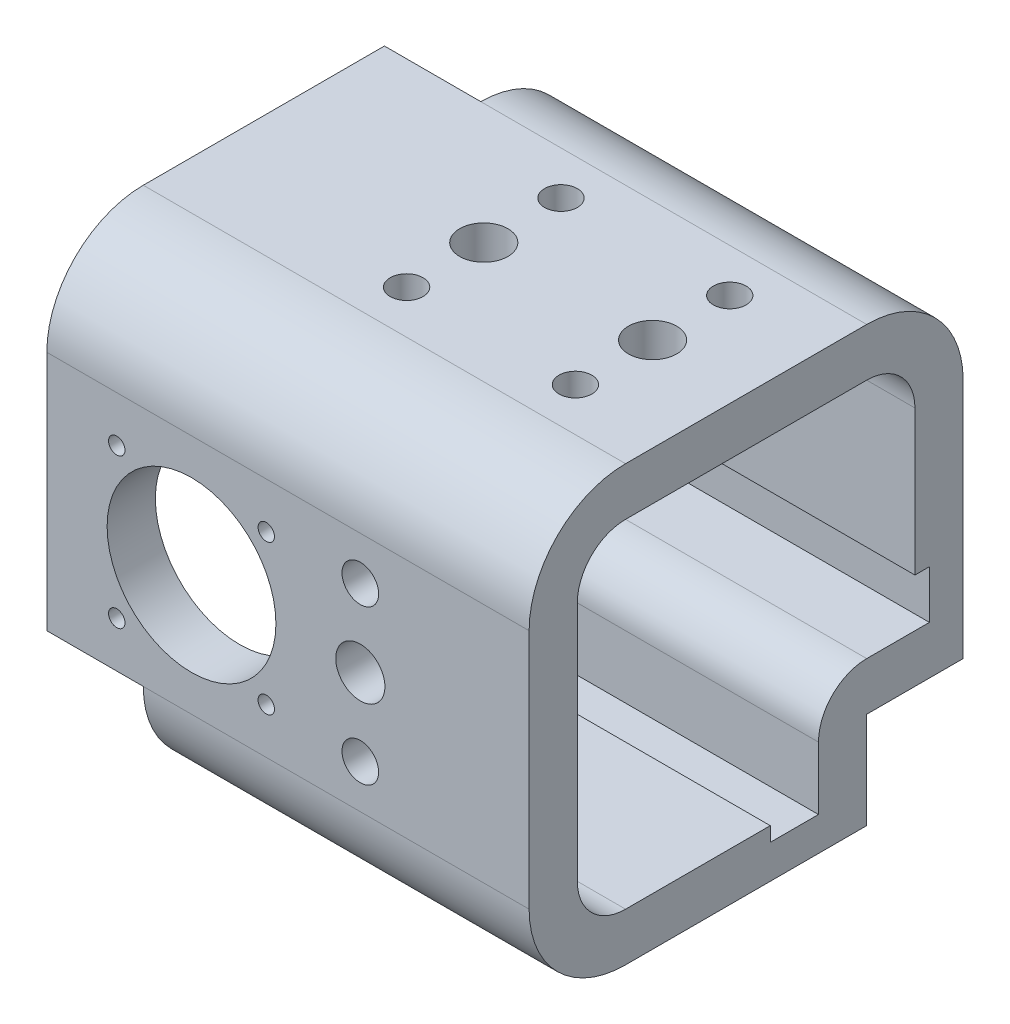
SolidWorks part; units mm, degrees
material "ABS"
ref_plane "Front Plane" through (0, 0, 0) normal (0, 0, 1) x (1, 0, 0)
ref_plane "Top Plane" through (0, 0, 0) normal (0, 1, 0) x (1, 0, 0)
ref_plane "Right Plane" through (0, 0, 0) normal (1, 0, 0) x (0, 0, -1)
sketch "Sketch2" plane through (0, 0, 0) normal (1, 0, 0) x (0, 0, -1)
  line L0 (3374.6539, 80.8979) -> (3374.6539, 76.9979) construction
  line L1 (3434.6539, 129.4479) -> (3384.6539, 129.4479)
  line L2 (3444.6539, 119.4479) -> (3444.6539, 69.4479)
  line L3 (3434.6539, 59.4479) -> (3384.6539, 59.4479)
  line L4 (3374.6539, 119.4479) -> (3374.6539, 69.4479)
  line L5 (-50.8, 109.4479) -> (3374.6539, 109.4479) construction
  line L10 (3367.4039, 109.4479) -> (3356.4039, 109.4479) construction
  line L11 (-50.8, 79.4479) -> (3374.6539, 79.4479) construction
  line L12 (3356.4039, 79.4479) -> (3367.4039, 79.4479) construction
  line L13 (3434.6539, 139.4479) -> (3384.6539, 139.4479)
  line L14 (3364.6539, 119.4479) -> (3364.6539, 69.4479)
  line L15 (3434.6539, 49.4479) -> (3384.6539, 49.4479)
  line L16 (3454.6539, 119.4479) -> (3454.6539, 69.4479)
  line L19 (3375.4039, 73.2979) -> (3386.4039, 73.2979) construction
  arc A0 (3384.6539, 129.4479) -> (3374.6539, 119.4479) centre (3384.6539, 119.4479) ccw
  arc A1 (3384.6539, 59.4479) -> (3374.6539, 69.4479) centre (3384.6539, 69.4479) cw
  arc A2 (3434.6539, 59.4479) -> (3444.6539, 69.4479) centre (3434.6539, 69.4479) ccw
  arc A3 (3434.6539, 129.4479) -> (3444.6539, 119.4479) centre (3434.6539, 119.4479) cw
  arc A4 (3384.6539, 139.4479) -> (3364.6539, 119.4479) centre (3384.6539, 119.4479) ccw
  arc A5 (3384.6539, 49.4479) -> (3364.6539, 69.4479) centre (3384.6539, 69.4479) cw
  arc A6 (3434.6539, 49.4479) -> (3454.6539, 69.4479) centre (3434.6539, 69.4479) ccw
  arc A7 (3434.6539, 139.4479) -> (3454.6539, 119.4479) centre (3434.6539, 119.4479) cw
  arc A8 (3434.6539, 129.4479) -> (3444.6539, 119.4479) centre (3434.6539, 119.4479) cw construction
  dimension "D1" = 10
  dimension "D2" = 10
  dimension "D3" = 3.85
  dimension "D4" = 70
extrude "Boss-Extrude1" add sketch "Sketch2" along normal blind 70 and the other way blind 30
sketch "Sketch3" plane through (0, 0, -3364.6539) normal (0, 0, 1) x (1, 0, 0)
  arc A0 (-14.0466, 99.7104) -> (-13.6647, 100.6346) centre (0, 94.4479) ccw construction
  arc A1 (-14.0466, 99.7104) -> (-13.6647, 100.6346) centre (0, 94.4479) ccw construction
  circle A2 centre (15.5, 78.9479) radius 1.7 construction
  circle A3 centre (15.5, 109.9479) radius 1.7 construction
  circle A4 centre (-15.5, 109.9479) radius 1.7 construction
  circle A5 centre (-15.5, 78.9479) radius 1.7 construction
  circle A6 centre (15.5, 78.9479) radius 1.7
  circle A7 centre (15.5, 109.9479) radius 1.7
  circle A8 centre (-15.5, 109.9479) radius 1.7
  circle A9 centre (-15.5, 78.9479) radius 1.7
  circle A10 centre (0, 94.4479) radius 17.5
  arc A11 (-16.3877, 100.5874) -> (-15.9422, 101.6657) centre (0, 94.4479) ccw construction
  circle A12 centre (35, 94.4479) radius 5.1 construction
  circle A13 centre (35, 94.4479) radius 5.1
  circle A14 centre (35, 78.4479) radius 3.8 construction
  circle A15 centre (35, 110.4479) radius 3.8 construction
  circle A16 centre (35, 78.4479) radius 3.8
  circle A17 centre (35, 110.4479) radius 3.8
  dimension "D1" = 2.5
extrude "Cut-Extrude1" cut sketch "Sketch3" against normal up to next
sketch "Sketch4" plane through (0, 139.4479, 0) normal (0, 1, 0) x (1, 0, 0)
  line L0 (50.6, 3409.6539) -> (15.6, 3409.6539) construction
  line L1 (-30, 3434.6539) -> (70, 3434.6539) construction
  line L2 (-30, 3384.6539) -> (70, 3384.6539) construction
  line L3 (28.05, 3396.5539) -> (38.15, 3396.5539) construction
  line L4 (28.05, 3396.5539) -> (38.15, 3396.5539) construction
  line L5 (33.1, 3396.5539) -> (33.1, 3409.6539) construction
  circle A0 centre (15.6, 3409.6539) radius 5
  circle A1 centre (50.6, 3409.6539) radius 5
  circle A2 centre (50.6, 3425.6539) radius 3.4 construction
  circle A3 centre (50.6, 3393.6539) radius 3.4 construction
  circle A4 centre (15.6, 3425.6539) radius 3.4 construction
  circle A5 centre (15.6, 3393.6539) radius 3.4 construction
  circle A6 centre (50.6, 3425.6539) radius 3.4
  circle A7 centre (50.6, 3393.6539) radius 3.4
  circle A8 centre (15.6, 3425.6539) radius 3.4
  circle A9 centre (15.6, 3393.6539) radius 3.4
  point P12 (33.1, 3409.6539)
  dimension "D1" = 10
  dimension "D2" = 35
extrude "Cut-Extrude2" cut sketch "Sketch4" against normal up to next
sketch "Sketch5" plane through (0, 0, -3364.6539) normal (0, 0, 1) x (1, 0, 0)
  line L0 (-30, 69.4479) -> (70, 69.4479) construction
  line L1 (-10, 69.4479) -> (-30, 69.4479)
  line L2 (-10, 69.4479) -> (-10, 49.4479)
  line L3 (-10, 49.4479) -> (-30, 49.4479)
  line L4 (-30, 69.4479) -> (-30, 49.4479)
  line L5 (-30, 119.4479) -> (-30, 69.4479) construction
  line L6 (-30, 49.4479) -> (70, 49.4479) construction
  dimension "D1" = 20
extrude "Cut-Extrude3" cut sketch "Sketch5" against normal through all both and the other way through all
sketch "Sketch6" plane through (0, 139.4479, 0) normal (0, 1, 0) x (1, 0, 0)
  line L0 (-30, 3434.6539) -> (-30, 3384.6539) construction
  line L1 (-30, 3454.6539) -> (-10, 3454.6539)
  line L2 (-30, 3454.6539) -> (-30, 3434.6539)
  line L3 (-30, 3434.6539) -> (-10, 3434.6539)
  line L4 (-10, 3454.6539) -> (-10, 3434.6539)
  line L5 (-30, 3434.6539) -> (70, 3434.6539) construction
  line L6 (-30, 3454.6539) -> (70, 3454.6539) construction
  dimension "D1" = 20
extrude "Cut-Extrude4" cut sketch "Sketch6" against normal through all
sketch "Sketch7" plane through (-10, 0, 0) normal (-1, 0, 0) x (0, 0, 1)
  line L10 (-3434.6539, 49.4479) -> (-3384.6539, 49.4479) construction
  line L11 (-3454.6539, 69.4479) -> (-3434.6539, 69.4479)
  line L12 (-3454.6539, 69.4479) -> (-3454.6539, 49.4479)
  line L13 (-3454.6539, 49.4479) -> (-3434.6539, 49.4479)
  line L14 (-3434.6539, 69.4479) -> (-3434.6539, 49.4479)
  line L15 (-3454.6539, 69.4479) -> (-3454.6539, 119.4479) construction
  line L16 (-3444.6539, 119.4479) -> (-3444.6539, 69.4479) construction
  line L17 (-3444.6539, 89.4479) -> (-3447.6539, 89.4479)
  line L18 (-3444.6539, 89.4479) -> (-3444.6539, 69.4479)
  line L19 (-3444.6539, 69.4479) -> (-3447.6539, 69.4479)
  line L20 (-3447.6539, 89.4479) -> (-3447.6539, 69.4479)
  line L21 (-3434.6539, 59.4479) -> (-3384.6539, 59.4479) construction
  line L22 (-3434.6539, 56.4479) -> (-3414.6539, 56.4479)
  line L23 (-3434.6539, 56.4479) -> (-3434.6539, 59.4479)
  line L24 (-3434.6539, 59.4479) -> (-3414.6539, 59.4479)
  line L25 (-3414.6539, 56.4479) -> (-3414.6539, 59.4479)
  dimension "D1" = 20
  dimension "D2" = 20
  dimension "D3" = 3
extrude "Cut-Extrude5" cut sketch "Sketch7" against normal through all
sketch "Sketch8" plane through (-10, 0, 0) normal (-1, 0, 0) x (0, 0, 1)
  line L0 (-3454.6539, 79.4479) -> (-3434.6539, 79.4479)
  line L1 (-3454.6539, 69.4479) -> (-3454.6539, 119.4479) construction
  line L2 (-3424.6539, 69.4479) -> (-3424.6539, 49.4479)
  line L3 (-3434.6539, 49.4479) -> (-3384.6539, 49.4479) construction
  line L4 (-3454.6539, 69.4479) -> (-3434.6539, 69.4479)
  line L5 (-3434.6539, 69.4479) -> (-3434.6539, 49.4479)
  line L8 (-3454.6539, 79.4479) -> (-3454.6539, 69.4479)
  line L9 (-3434.6539, 49.4479) -> (-3424.6539, 49.4479)
  line L10 (-3424.6539, 79.4479) -> (-3424.6539, 49.4479) construction
  line L11 (-3454.6539, 79.4479) -> (-3424.6539, 79.4479) construction
  line L12 (-3454.6539, 69.4479) -> (-3447.6539, 69.4479) construction
  line L13 (-3434.6539, 56.4479) -> (-3434.6539, 49.4479) construction
  arc A0 (-3424.6539, 69.4479) -> (-3434.6539, 79.4479) centre (-3434.6539, 69.4479) ccw
  dimension "D2" = 10
  dimension "D1" = 10
extrude "Boss-Extrude2" add sketch "Sketch8" against normal up to surface (80 mm away) up to face at (70, 90.4586, -3413.6433)
